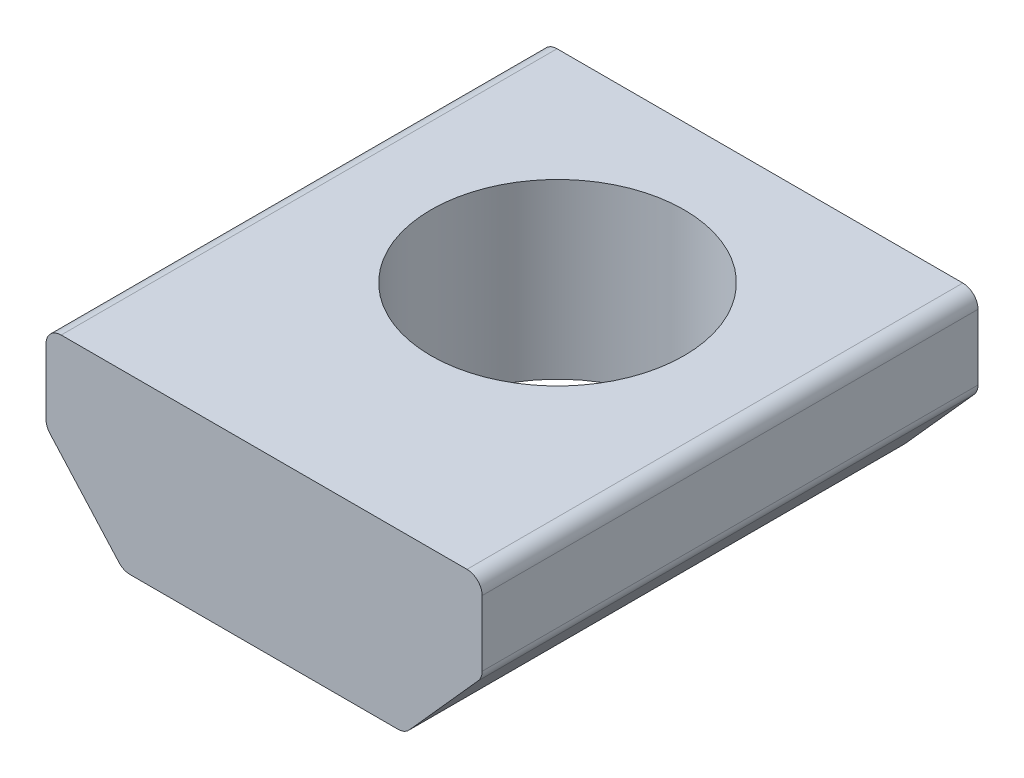
SolidWorks part; units mm, degrees
material "AISI 1020"
ref_plane "Front Plane" through (0, 0, 0) normal (0, 0, 1) x (1, 0, 0)
ref_plane "Top Plane" through (0, 0, 0) normal (0, 1, 0) x (1, 0, 0)
ref_plane "Right Plane" through (0, 0, 0) normal (1, 0, 0) x (0, 0, -1)
sketch "Sketch1" plane through (0, 0, 0) normal (0, 0, 1) x (1, 0, 0)
  line L0 (-5.0927, 0) -> (5.0927, 0)
  line L1 (5.4737, -0.381) -> (5.4737, -2.0261)
  line L2 (-5.4737, -0.381) -> (-5.4737, -2.0261)
  line L3 (-3.3603, -4.3434) -> (3.3603, -4.3434)
  line L4 (-3.6442, -4.2164) -> (-5.3766, -2.2802)
  line L5 (3.6442, -4.2164) -> (5.3766, -2.2802)
  arc A0 (-5.0927, 0) -> (-5.4737, -0.381) centre (-5.0927, -0.381) ccw
  arc A1 (-5.4737, -2.0261) -> (-5.3766, -2.2802) centre (-5.0927, -2.0261) ccw
  arc A2 (-3.6442, -4.2164) -> (-3.3603, -4.3434) centre (-3.3603, -3.9624) ccw
  arc A3 (3.3603, -4.3434) -> (3.6442, -4.2164) centre (3.3603, -3.9624) ccw
  arc A4 (5.3766, -2.2802) -> (5.4737, -2.0261) centre (5.0927, -2.0261) ccw
  arc A5 (5.4737, -0.381) -> (5.0927, 0) centre (5.0927, -0.381) ccw
  point P18 (0, 0)
extrude "Extrude1" add sketch "Sketch1" along normal blind 12.446
sketch "Sketch2" plane through (0, 0, 0) normal (0, 1, 0) x (-1, 0, 0)
  line L0 (0, 0) -> (0, 12.446) construction
  line L1 (-5.0927, 0) -> (5.0927, 0) construction
  line L2 (-5.0927, 12.446) -> (5.0927, 12.446) construction
  circle A0 centre (0, 5.08) radius 3.175
  dimension "D2" = 6.35
  dimension "D1" = 5.08
extrude "Cut-Extrude1" cut sketch "Sketch2" against normal blind 12.446
